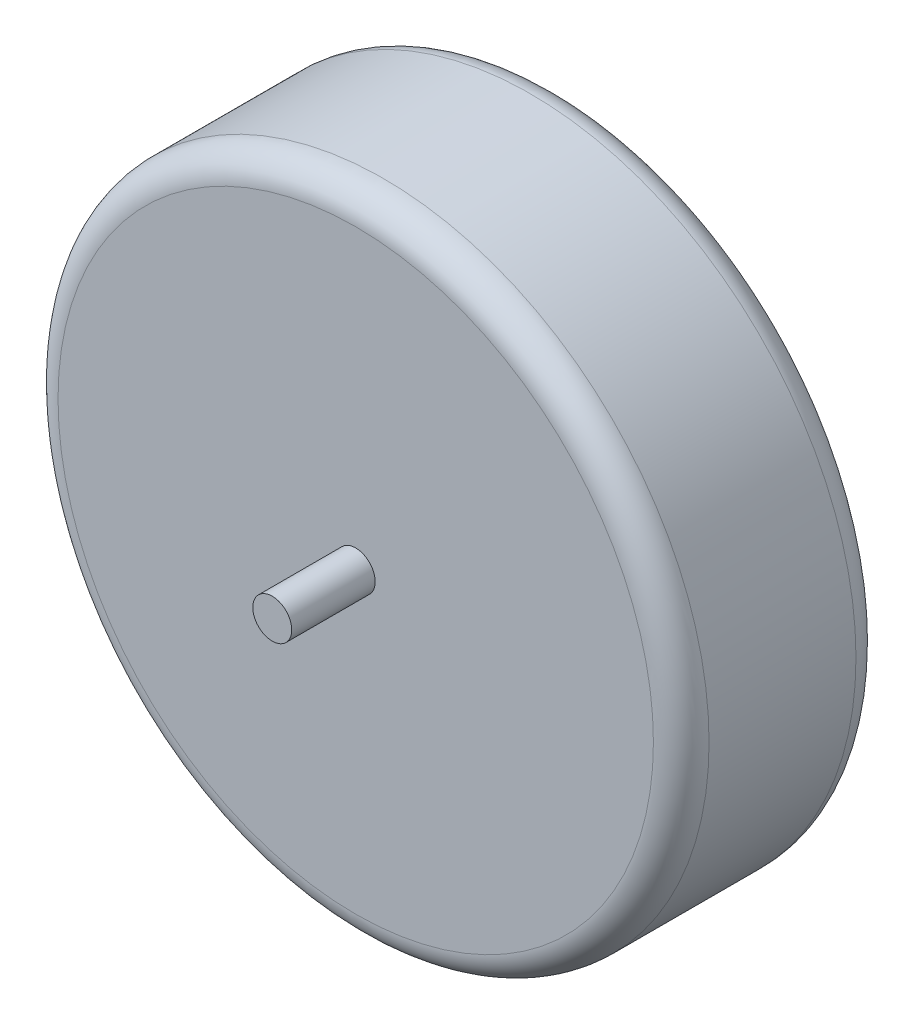
SolidWorks part; units mm, degrees
ref_plane "Front Plane" through (0, 0, 0) normal (0, 0, 1) x (1, 0, 0)
ref_plane "Top Plane" through (0, 0, 0) normal (0, 1, 0) x (1, 0, 0)
ref_plane "Right Plane" through (0, 0, 0) normal (1, 0, 0) x (0, 0, -1)
sketch "Sketch1" plane through (0, 0, 0) normal (0, 0, 1) x (1, 0, 0)
  line L0 (-16.6872, 0) -> (121.8554, 0) construction
  line L1 (0, 76.2567) -> (0, -67.3309) construction
  circle A0 centre (0, 0) radius 74.295
  dimension "D1" = 148.59
extrude "Boss-Extrude1" add sketch "Sketch1" along normal blind 46.228
fillet "Fillet1" radius 6.35 2 edges at (74.295, 0, 0) (74.295, 0, 46.228)
sketch "Sketch2" plane through (0, 0, 46.228) normal (0, 0, 1) x (1, 0, 0)
  circle A0 centre (0, 0) radius 4.445
  dimension "D1" = 8.89
extrude "Boss-Extrude2" add sketch "Sketch2" along normal blind 19.05 and the other way blind 65.278
ref_plane "Plane1" through (0, 0, 23.114) normal (0, 0, 1) x (1, 0, 0)
